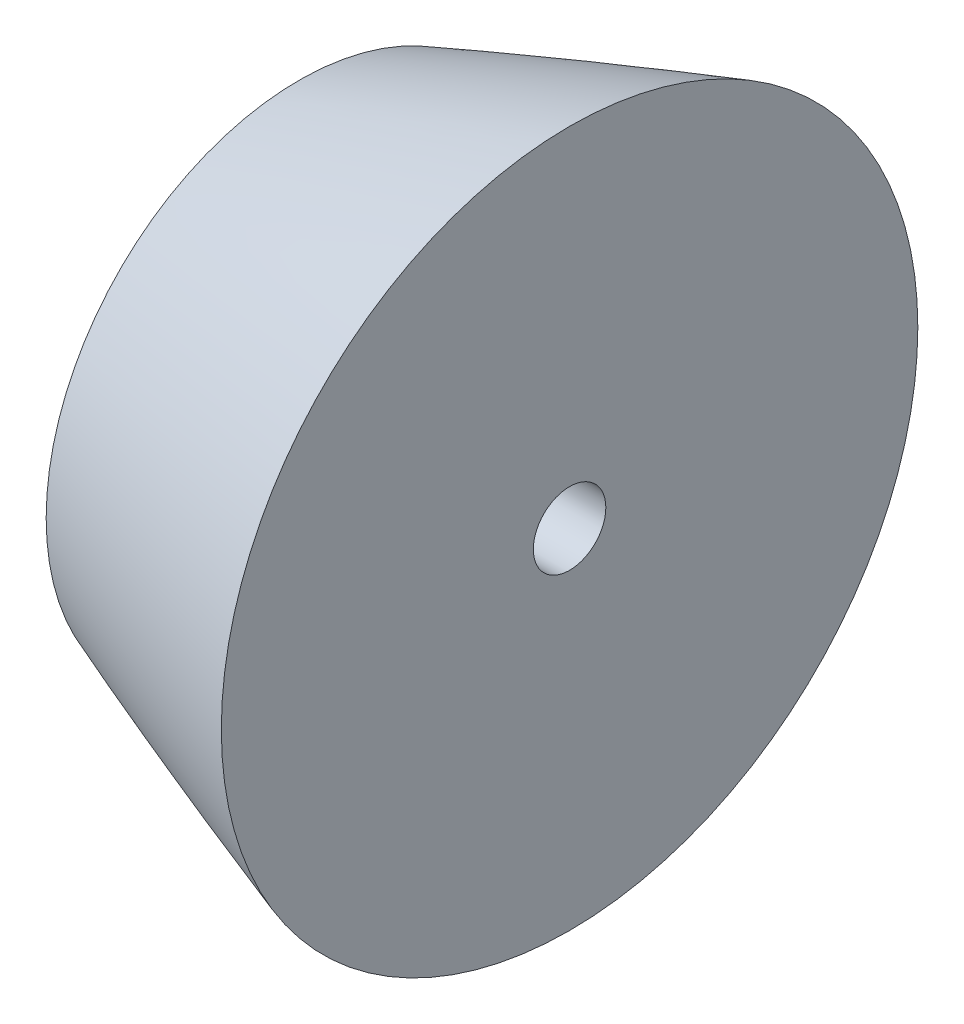
SolidWorks part; units mm, degrees
material "6061-T6 (SS)"
ref_plane "Front Plane" through (0, 0, 0) normal (0, 0, 1) x (1, 0, 0)
ref_plane "Top Plane" through (0, 0, 0) normal (0, 1, 0) x (1, 0, 0)
ref_plane "Right Plane" through (0, 0, 0) normal (1, 0, 0) x (0, 0, -1)
sketch "Sketch1" plane through (0, 0, 0) normal (0, 0, 1) x (1, 0, 0)
  line L0 (0, 0) -> (457.2, 0)
  line L2 (457.2, 95.25) -> (457.2, 0) construction
  line L5 (457.2, 0) -> (471.3928, 0)
  line L7 (457.2, 95.25) -> (471.3928, 95.25)
  line L8 (471.3928, 0) -> (471.3928, 95.25)
  line L15 (457.2, 0) -> (-3.2335, 0) construction
  line L20 (-3.2335, 0) -> (0, 0) construction
  spline S0 degree 4 poles (0, 0) (0.0023, 0.0126) (0.0082, 0.0373) (0.0262, 0.085) (0.0706, 0.1767) (0.1354, 0.2842) (0.2204, 0.4066) (0.336, 0.5565) (0.5083, 0.7608) (0.8021, 1.0733) (1.3251, 1.5652) (2.2381, 2.3192) (3.8253, 3.4666) (6.614, 5.2253) (11.4561, 7.8766) (19.2936, 11.6017) (32.6156, 17.1305) (51.6883, 23.9819) (75.6131, 31.5462) (103.3102, 39.362) (131.8924, 46.6864) (160.6143, 53.4403) (189.4482, 59.6969) (218.3767, 65.4994) (247.3876, 70.874) (276.4727, 75.8318) (305.6259, 80.3722) (334.843, 84.4812) (364.1216, 88.1294) (389.7928, 90.8706) (411.8341, 92.8374) (428.9951, 94.0676) (440.0323, 94.6976) (448.6181, 95.062) (453.5214, 95.2002) (455.9737, 95.2443) (457.2, 95.25) knots 0 0 0 0 0 0.000108 0.000216 0.000433 0.000866 0.001175 0.001483 0.002044 0.003139 0.004822 0.007588 0.012112 0.019791 0.032854 0.05453 0.085907 0.142462 0.205216 0.267971 0.330725 0.393479 0.456233 0.518987 0.581741 0.644496 0.70725 0.770004 0.832758 0.895512 0.926889 0.958267 0.979133 0.989567 1 1 1 1 1 construction
  spline S1 degree 4 poles (0, 0) (0.0023, 0.0126) (0.0082, 0.0373) (0.0262, 0.085) (0.0706, 0.1767) (0.1354, 0.2842) (0.2204, 0.4066) (0.336, 0.5565) (0.5083, 0.7608) (0.8021, 1.0733) (1.3251, 1.5652) (2.2381, 2.3192) (3.8253, 3.4666) (6.614, 5.2253) (11.4561, 7.8766) (19.2936, 11.6017) (32.6156, 17.1305) (51.6883, 23.9819) (75.6131, 31.5462) (103.3102, 39.362) (131.8924, 46.6864) (160.6143, 53.4403) (189.4482, 59.6969) (218.3767, 65.4994) (247.3876, 70.874) (276.4727, 75.8318) (305.6259, 80.3722) (334.843, 84.4812) (364.1216, 88.1294) (389.7928, 90.8706) (411.8341, 92.8374) (428.9951, 94.0676) (440.0323, 94.6976) (448.6181, 95.062) (453.5214, 95.2002) (455.9737, 95.2443) (457.2, 95.25) knots 0 0 0 0 0 0.000108 0.000216 0.000433 0.000866 0.001175 0.001483 0.002044 0.003139 0.004822 0.007588 0.012112 0.019791 0.032854 0.05453 0.085907 0.142462 0.205216 0.267971 0.330725 0.393479 0.456233 0.518987 0.581741 0.644496 0.70725 0.770004 0.832758 0.895512 0.926889 0.958267 0.979133 0.989567 1 1 1 1 1
  dimension "D1" = 457.2
revolve "Revolve3" add sketch "Sketch1" angle 360 about L0
ref_plane "Plane1" through (-3.2335, 0, 0) normal (1, 0, 0) x (0, 0, -1)
ref_plane "Plane2" through (34.8665, 0, 0) normal (1, 0, 0) x (0, 0, -1)
sketch "Sketch2" plane through (34.8665, 0, 0) normal (1, 0, 0) x (0, 0, -1)
  circle A2 centre (0, 0) radius 95.25 construction
  circle A3 centre (0, 0) radius 95.25
ref_plane "Plane3" through (53.9165, 0, 0) normal (1, 0, 0) x (0, 0, -1)
sketch "Sketch4" plane through (53.9165, 0, 0) normal (1, 0, 0) x (0, 0, -1)
  circle A0 centre (0, 0) radius 95.25 construction
  circle A1 centre (0, 0) radius 95.25
extrude "Cut-Extrude2" cut sketch "Sketch4" along normal through all
extrude "Cut-Extrude3" cut sketch "Sketch2" against normal through all contours A3
hole_wizard "1/4-20 Tapped Hole1" positions "Sketch5" profile "Sketch6" tap size "1/4-20" standard "ANSI Inch" end condition through all
sketch "Sketch5" plane through (53.9165, 0, 0) normal (1, 0, 0) x (0, 0, -1)
  point P0 (0, 0)
sketch "Sketch6" plane through (53.9165, 0, 0) normal (0, 1, 0) x (0, 0, -1)
  line L0 (0, 0) -> (0, 19.05)
  line L1 (0, 19.05) -> (2.5527, 19.05)
  line L2 (2.5527, 19.05) -> (2.5527, 0)
  line L5 (2.5527, 0) -> (0, 0)
  line L11 (0, -6.35) -> (0, 107.95) construction
  dimension "Thru Tap Drill Dia." = 5.1054
  dimension "Thru Tap Drill Depth" = 19.05
cosmetic thread "Hole Thread1" parameters "D2"=6.35
